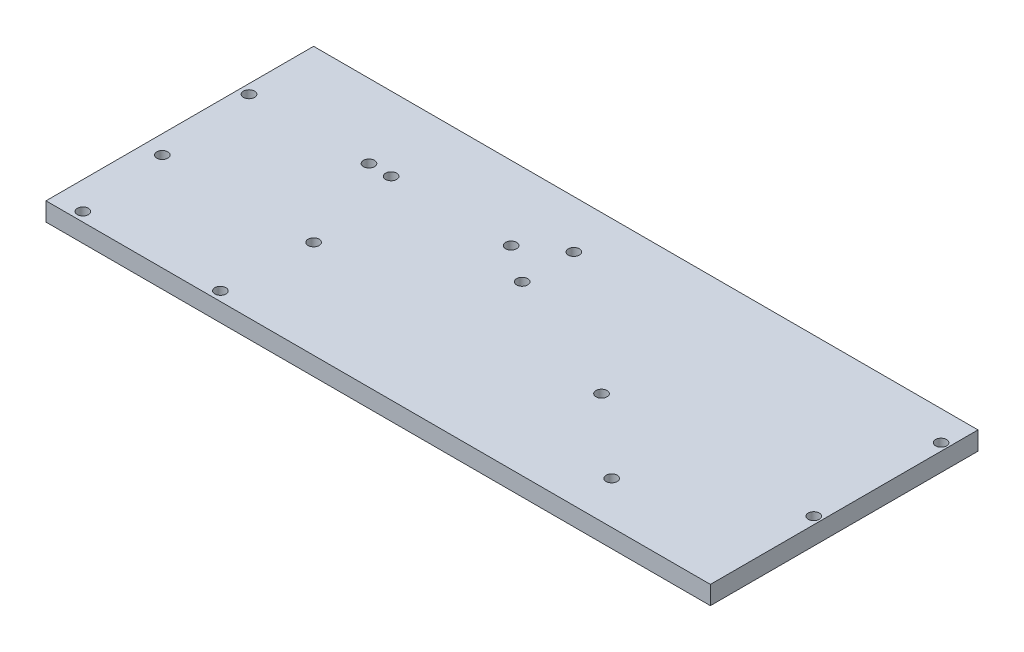
SolidWorks part; units mm, degrees
ref_plane "Front Plane" through (0, 0, 0) normal (0, 0, 1) x (1, 0, 0)
ref_plane "Top Plane" through (0, 0, 0) normal (0, 1, 0) x (1, 0, 0)
ref_plane "Right Plane" through (0, 0, 0) normal (1, 0, 0) x (0, 0, -1)
sketch "Sketch1" plane through (0, 0, 0) normal (0, 1, 0) x (1, 0, 0)
  line L1 (0, 0) -> (360, 0)
  line L2 (0, 0) -> (0, 145)
  line L3 (0, 145) -> (360, 145)
  line L4 (360, 0) -> (360, 145)
  line L5 (360, 0) -> (225, 0)
  line L6 (360, 0) -> (360, 135)
  line L7 (360, 135) -> (225, 135)
  line L8 (225, 0) -> (225, 135)
  circle A0 centre (15, 5) radius 3
  circle A1 centre (10, 53) radius 3
  circle A2 centre (92, 53) radius 3
  circle A3 centre (89.5, 5) radius 3
  circle A4 centre (5, 105) radius 3
  circle A5 centre (70, 105) radius 3
  circle A6 centre (82, 105) radius 3
  circle A7 centre (147, 105) radius 3
  circle A8 centre (356, 60) radius 3
  circle A9 centre (356, 129) radius 3
  circle A10 centre (241, 60) radius 3
  circle A11 centre (283.5, 23) radius 3
  circle A12 centre (167, 91) radius 3
  circle A13 centre (167, 119) radius 3
  point P32 (0, 0)
  dimension "D3" = 6
  dimension "D6" = 6
  dimension "D10" = 6
  dimension "D12" = 6
  dimension "D13" = 6
  dimension "D17" = 6
  dimension "D20" = 6
  dimension "D21" = 6
  dimension "D22" = 6
  dimension "D29" = 6
  dimension "D30" = 6
  dimension "D31" = 115
  dimension "D34" = 6
  dimension "D35" = 6
  dimension "D36" = 6
  dimension "D1" = 360
  dimension "D2" = 145
  dimension "D4" = 5
  dimension "D5" = 15
  dimension "D7" = 10
  dimension "D8" = 48
  dimension "D9" = 74.5
  dimension "D11" = 82
  dimension "D14" = 40
  dimension "D15" = 5
  dimension "D16" = 65
  dimension "D18" = 12
  dimension "D19" = 65
  dimension "D23" = 4
  dimension "D24" = 60
  dimension "D25" = 135
  dimension "D26" = 135
  dimension "D27" = 4
  dimension "D28" = 6
  dimension "D32" = 72.5
  dimension "D33" = 37
  dimension "D37" = 28
  dimension "D38" = 14
  dimension "D39" = 20
extrude "Boss-Extrude1" add sketch "Sketch1" along normal blind 10 contours L1 L8 L7 L4 L3 L2 A7 A6 A5 A4 A3 A2 A1 A0 | L8 L1 L4 L7 A9 A8
